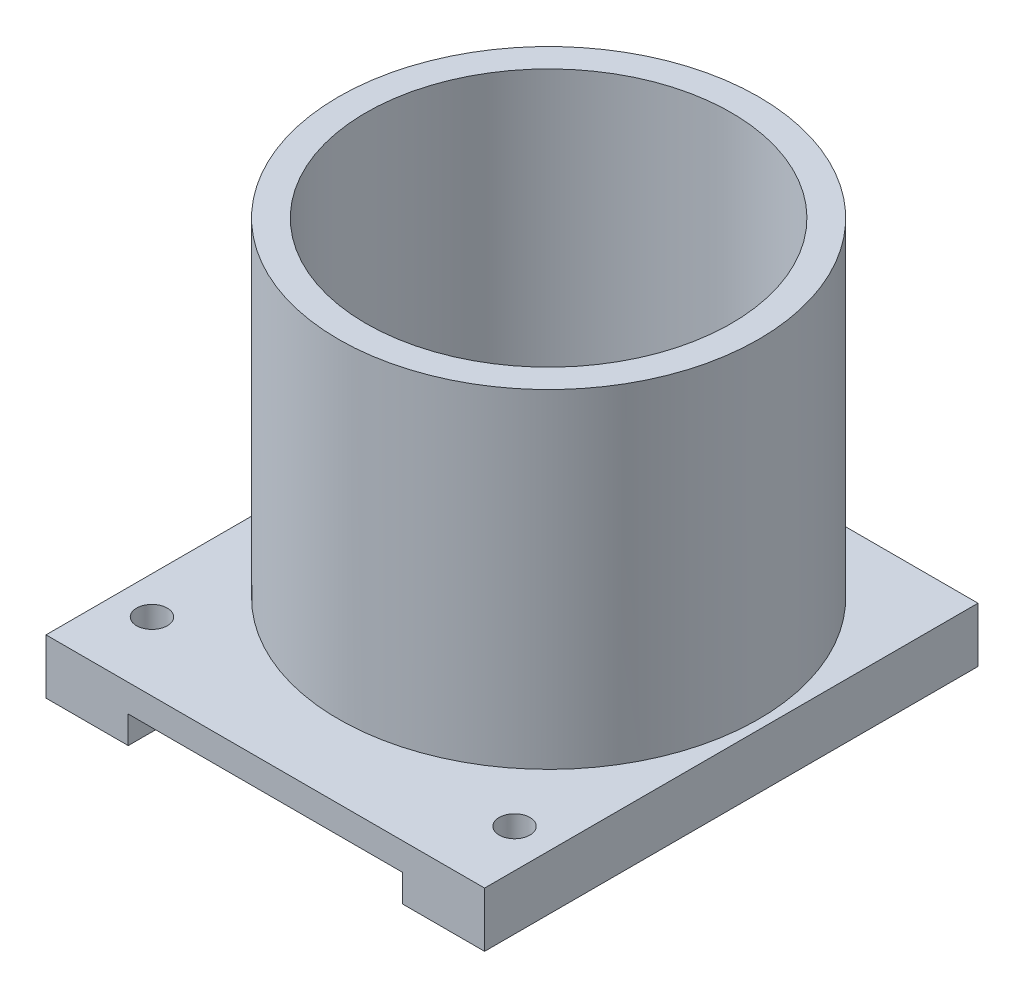
SolidWorks part; units mm, degrees
ref_plane "Front Plane" through (0, 0, 0) normal (0, 0, 1) x (1, 0, 0)
ref_plane "Top Plane" through (0, 0, 0) normal (0, 1, 0) x (1, 0, 0)
ref_plane "Right Plane" through (0, 0, 0) normal (1, 0, 0) x (0, 0, -1)
sketch "Sketch1" plane through (0, 0, 0) normal (0, 1, 0) x (1, 0, 0)
  circle A0 centre (0, 0) radius 12.1666
  circle A1 centre (0, 0) radius 10.5791
  dimension "D1" = 24.3332
  dimension "D2" = 1.5875
extrude "Boss-Extrude1" add sketch "Sketch1" along normal blind 19.05
sketch "Sketch2" plane through (0, 0, 0) normal (0, -1, 0) x (1, 0, 0)
  line L1 (-12.7, 16.4084) -> (12.7, 16.4084)
  line L2 (-12.7, 16.4084) -> (-12.7, -12.1666)
  line L3 (-12.7, -12.1666) -> (12.7, -12.1666)
  line L4 (12.7, 16.4084) -> (12.7, -12.1666)
  line L5 (-12.7, 16.4084) -> (12.7, -12.1666) construction
  line L6 (-12.7, -12.1666) -> (12.7, 16.4084) construction
  circle A0 centre (0, 0) radius 12.1666 construction
  point P0 (0, 2.1209)
  dimension "D1" = 25.4
  dimension "D2" = 28.575
extrude "Boss-Extrude2" add sketch "Sketch2" along normal blind 3.175
sketch "Sketch3" plane through (0, -3.175, 0) normal (0, -1, 0) x (1, 0, 0)
  circle A0 centre (0, 0) radius 6.35
  dimension "D1" = 12.7
extrude "Cut-Extrude1" cut sketch "Sketch3" against normal through all
sketch "Sketch8" plane through (0, 0, 0) normal (0, 1, 0) x (1, 0, 0)
  circle A0 centre (0, 0) radius 10.5791 construction
  circle A1 centre (0, 0) radius 6.35 construction
  circle A2 centre (0, 0) radius 10.5791
  circle A3 centre (0, 0) radius 6.35
extrude "Boss-Extrude4" add sketch "Sketch8" along normal offset from surface (0.127 mm away) 3.302 up to face at (0, -3.175, -6.35)
sketch "Sketch9" plane through (0, 0.127, 0) normal (0, 1, 0) x (1, 0, 0)
  circle A0 centre (0, 0) radius 10.5791 construction
  circle A1 centre (0, 0) radius 10.5791
  circle A2 centre (0, 0) radius 3.9688
  dimension "D1" = 7.9375
extrude "Boss-Extrude5" add sketch "Sketch9" along normal blind 3.175
hole_wizard "#2-56 Tapped Hole1" positions "Sketch4" profile "Sketch5" tap size "#2-56" standard "ANSI Inch"
sketch "Sketch4" plane through (0, -3.175, 0) normal (0, -1, 0) x (-1, 0, 0)
  point P0 (10.5315, -12.4414)
  point P2 (10.5315, 0.0586)
  point P4 (-10.4685, -12.4414)
  point P6 (-10.4685, 0.0586)
sketch "Sketch5" plane through (-10.5315, -3.175, 12.4414) normal (1, 0, 0) x (0, 0, -1)
  line L0 (0, 0) -> (0, 6.1222)
  line L1 (0, 6.1222) -> (0.889, 5.588)
  line L2 (0.889, 5.588) -> (0.889, 0)
  line L3 (0.889, 0) -> (0, 0)
  line L4 (0, 6.1222) -> (-0.889, 5.588) construction
  line L5 (0, -6.35) -> (0, 107.95) construction
  dimension "Tap Drill Dia." = 1.778
  dimension "Tap Drill Depth" = 5.588
  dimension "Drill Angle" = 118
cosmetic thread "Hole Thread1" parameters "D1"=4.318, "D2"=2.1844
cosmetic thread "Hole Thread2" parameters "D1"=3.175, "D2"=2.1844
cosmetic thread "Hole Thread3" parameters "D1"=4.318, "D2"=2.1844
cosmetic thread "Hole Thread4" parameters "D1"=3.175, "D2"=2.1844
sketch "Sketch6" plane through (0, -3.175, 0) normal (0, -1, 0) x (1, 0, 0)
  line L1 (-7.9375, 18.5411) -> (7.9375, 18.5411)
  line L2 (-7.9375, 18.5411) -> (-7.9375, -18.5411)
  line L3 (-7.9375, -18.5411) -> (7.9375, -18.5411)
  line L4 (7.9375, 18.5411) -> (7.9375, -18.5411)
  line L5 (-7.9375, 18.5411) -> (7.9375, -18.5411) construction
  line L6 (-7.9375, -18.5411) -> (7.9375, 18.5411) construction
  point P0 (0, 0)
  dimension "D1" = 15.875
extrude "Cut-Extrude2" cut sketch "Sketch6" against normal blind 1.5875
